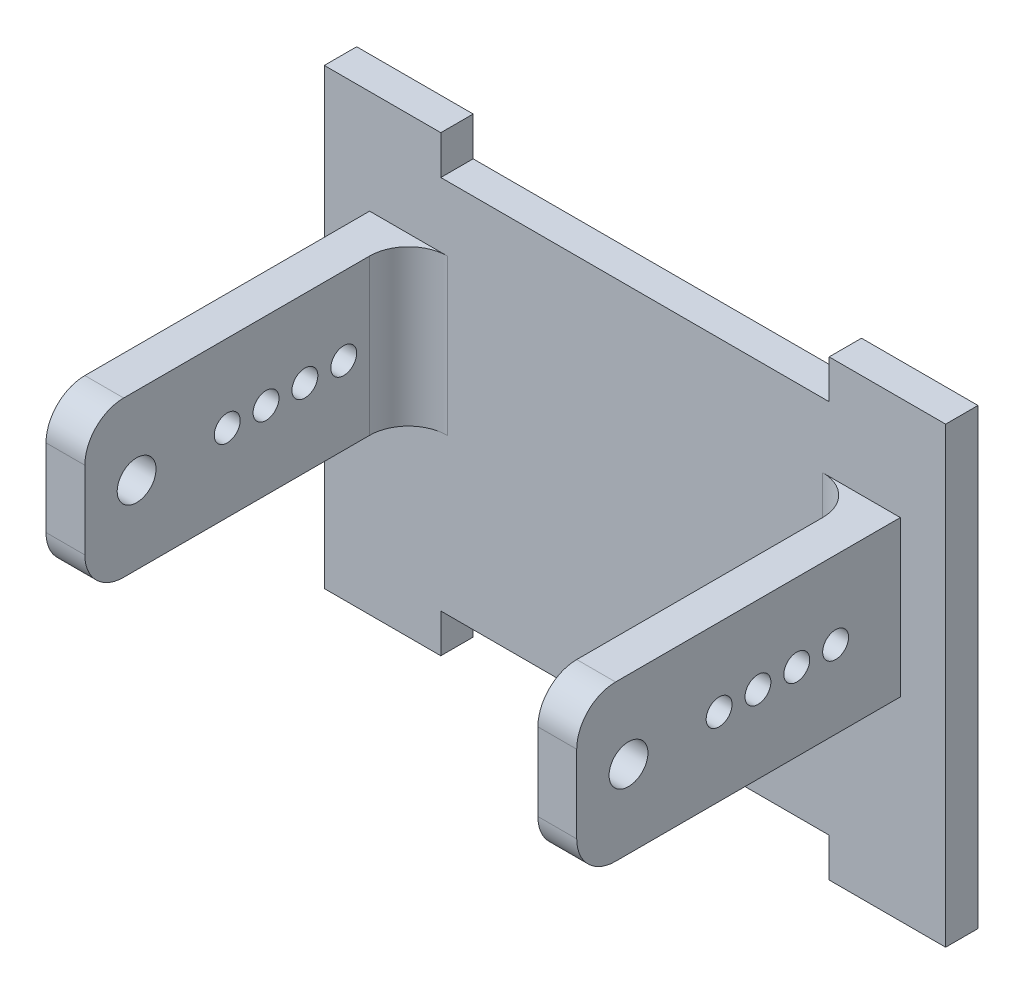
SolidWorks part; units mm, degrees
ref_plane "Plan de face" through (0, 0, 0) normal (0, 0, 1) x (1, 0, 0)
ref_plane "Plan de dessus" through (0, 0, 0) normal (0, 1, 0) x (1, 0, 0)
ref_plane "Plan de droite" through (0, 0, 0) normal (1, 0, 0) x (0, 0, -1)
sketch "Esquisse1" plane through (0, 0, 0) normal (0, 0, 1) x (1, 0, 0)
  line L0 (39, 35) -> (48, 35)
  line L1 (0, 0) -> (9, 0)
  line L2 (0, 0) -> (0, 35)
  line L3 (0, 35) -> (9, 35)
  line L4 (48, 0) -> (48, 35)
  line L5 (39, 0) -> (48, 0)
  line L6 (9, 35) -> (9, 32)
  line L7 (9, 32) -> (39, 32)
  line L8 (39, 35) -> (39, 32)
  line L10 (9, 0) -> (9, 3)
  line L11 (9, 3) -> (39, 3)
  line L12 (39, 0) -> (39, 3)
  dimension "D1" = 48
  dimension "D2" = 35
  dimension "D3" = 30
  dimension "D4" = 30
  dimension "D5" = 3
  dimension "D6" = 3
  dimension "D7" = 9
  dimension "D8" = 9
extrude "Boss.-Extru.1" add sketch "Esquisse1" along normal blind 2.5
sketch "Esquisse2" plane through (0, 0, 2.5) normal (0, 0, 1) x (1, 0, 0)
  line L1 (3.5, 27) -> (6.5, 27)
  line L2 (3.5, 27) -> (3.5, 15)
  line L3 (3.5, 15) -> (6.5, 15)
  line L4 (6.5, 27) -> (6.5, 15)
  line L5 (41.5, 27) -> (44.5, 27)
  line L6 (41.5, 27) -> (41.5, 15)
  line L7 (41.5, 15) -> (44.5, 15)
  line L8 (44.5, 27) -> (44.5, 15)
  line L9 (9, 35) -> (0, 35) construction
  line L11 (0, 35) -> (0, 0) construction
  dimension "D1" = 3
  dimension "D2" = 12
  dimension "D3" = 3
  dimension "D4" = 12
  dimension "D5" = 3.5
  dimension "D6" = 35
  dimension "D7" = 8
  dimension "D8" = 8
extrude "Boss.-Extru.2" add sketch "Esquisse2" along normal blind 25
sketch "Esquisse3" plane through (44.5, 0, 0) normal (1, 0, 0) x (0, 0, -1)
  line L0 (-27.5, 27) -> (-2.5, 27) construction
  line L1 (-2.5, 15) -> (-2.5, 27) construction
  circle A0 centre (-7.5, 21) radius 1
  circle A1 centre (-10.5, 21) radius 1
  circle A2 centre (-13.5, 21) radius 1
  circle A3 centre (-16.5, 21) radius 1
  circle A4 centre (-23.5, 21) radius 1.5
  dimension "D1" = 2
  dimension "D2" = 2
  dimension "D3" = 2
  dimension "D4" = 2
  dimension "D5" = 6
  dimension "D6" = 6
  dimension "D7" = 6
  dimension "D8" = 6
  dimension "D9" = 5
  dimension "D10" = 3
  dimension "D11" = 3
  dimension "D12" = 3
  dimension "D13" = 3
  dimension "D14" = 16
  dimension "D15" = 6
extrude "Enlèv. mat.-Extru.1" cut sketch "Esquisse3" against normal blind 50
fillet "Congé1" radius 3 4 edges at (43, 15, 27.5) (43, 27, 27.5) (5, 15, 27.5) (5, 27, 27.5)
fillet "Congé2" radius 3 2 edges at (41.5, 21, 2.5) (6.5, 21, 2.5)
